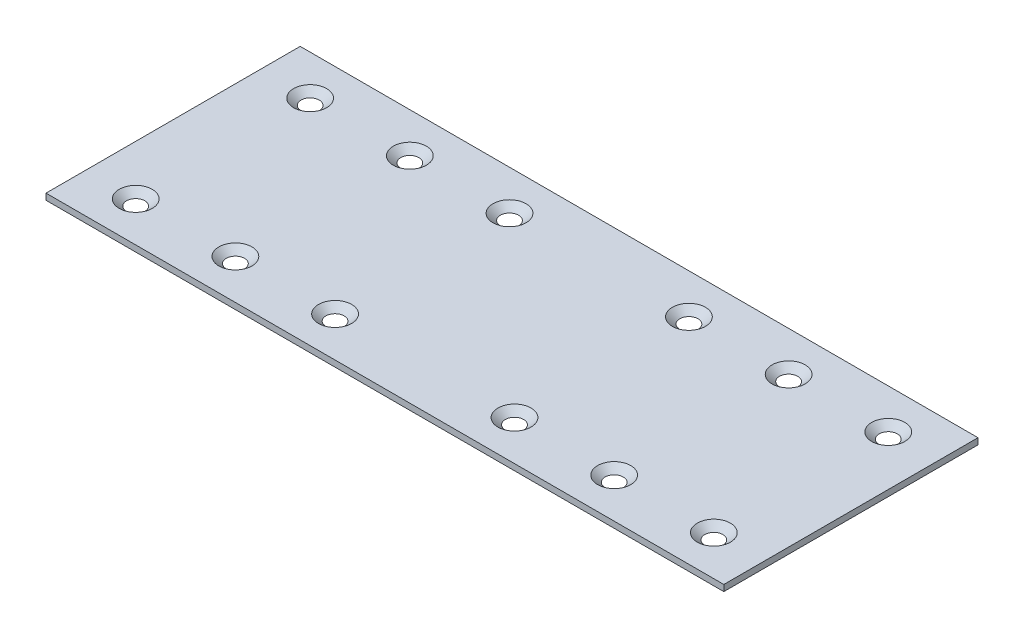
SolidWorks part; units mm, degrees
ref_plane "Front Plane" through (0, 0, 0) normal (0, 0, 1) x (1, 0, 0)
ref_plane "Top Plane" through (0, 0, 0) normal (0, 1, 0) x (1, 0, 0)
ref_plane "Right Plane" through (0, 0, 0) normal (1, 0, 0) x (0, 0, -1)
sketch "Sketch1" plane through (0, 0, 0) normal (0, 1, 0) x (1, 0, 0)
  line L1 (0, 0) -> (172.72, 0)
  line L2 (0, 0) -> (0, 64.77)
  line L3 (0, 64.77) -> (172.72, 64.77)
  line L4 (172.72, 0) -> (172.72, 64.77)
  dimension "D1" = 172.72
  dimension "D2" = 64.77
extrude "Boss-Extrude1" add sketch "Sketch1" along normal blind 1.5875
hole_wizard "CSK for #8 Flat Head Machine Screw (100)1" positions "Sketch3" profile "Sketch4" countersink size "#8" standard "ANSI Inch"
sketch "Sketch3" plane through (0, 1.5875, 0) normal (0, 1, 0) x (1, 0, 0)
  line L1 (172.72, 0) -> (172.72, 64.77) construction
  line L2 (0, 0) -> (172.72, 0) construction
  line L3 (172.72, 64.77) -> (0, 64.77) construction
  line L4 (0, 64.77) -> (0, 0) construction
  point P0 (12.7, 54.61)
  point P3 (38.1, 54.61)
  point P6 (63.5, 54.61)
  point P9 (109.22, 54.61)
  point P12 (134.62, 54.61)
  point P15 (160.02, 54.61)
  point P18 (160.02, 10.16)
  point P21 (134.62, 10.16)
  point P24 (109.22, 10.16)
  point P27 (63.5, 10.16)
  point P30 (38.1, 10.16)
  point P33 (12.7, 10.16)
  dimension "D1" = 12.7
  dimension "D2" = 10.16
  dimension "D3" = 10.16
  dimension "D4" = 25.4
  dimension "D5" = 25.4
  dimension "D6" = 12.7
  dimension "D7" = 25.4
  dimension "D8" = 25.4
sketch "Sketch4" plane through (12.7, 1.5875, -54.61) normal (1, 0, 0) x (0, 0, 1)
  line L0 (0, 0) -> (0, 14.0507)
  line L1 (0, 14.0507) -> (2.2479, 12.7)
  line L2 (2.2479, 12.7) -> (2.2479, 1.6518)
  line L3 (2.2479, 1.6518) -> (4.2164, 0)
  line L5 (4.2164, 0) -> (0, 0)
  line L6 (-2.2479, 1.6518) -> (-4.2164, 0) construction
  line L10 (0, 14.0507) -> (-2.2479, 12.7) construction
  line L11 (0, -6.35) -> (0, 107.95) construction
  dimension "Hole Dia." = 4.4958
  dimension "Hole Depth" = 12.7
  dimension "Near C'Sink Dia." = 8.4328
  dimension "Near C'Sink Angle" = 100
  dimension "Drill Angle" = 118
